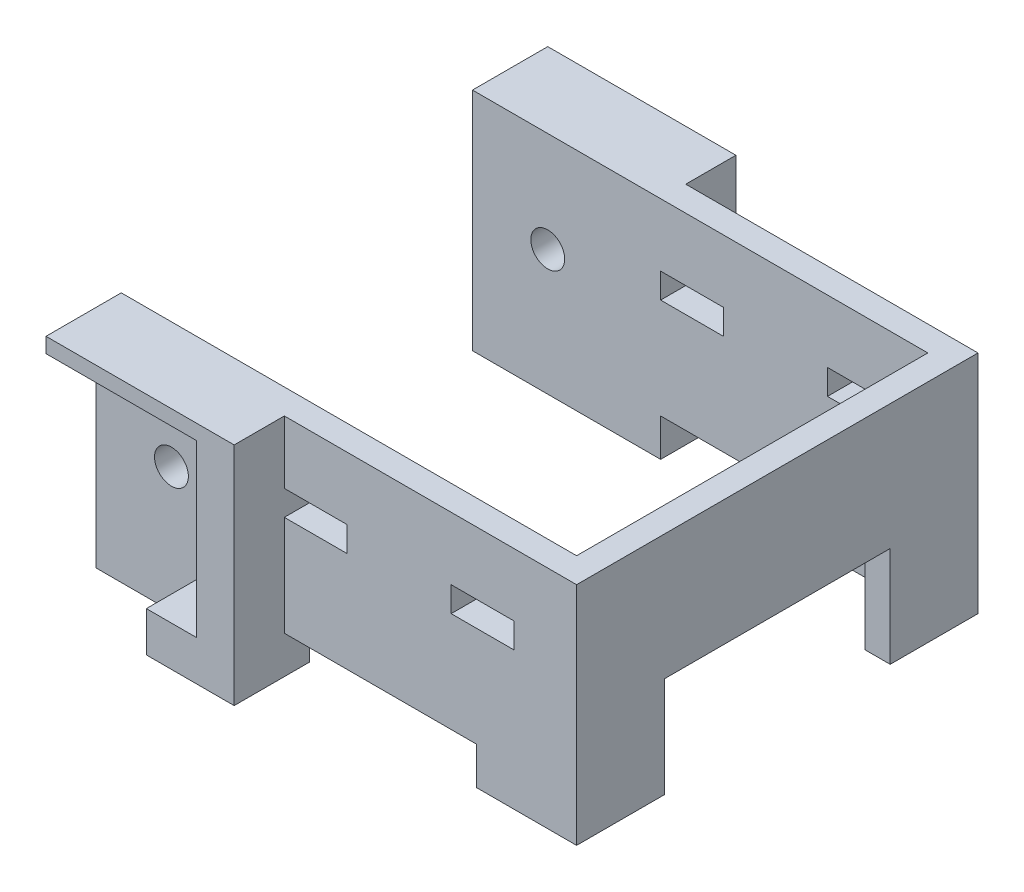
SolidWorks part; units mm, degrees
material "ABS"
ref_plane "Спереди" through (0, 0, 0) normal (0, 0, 1) x (1, 0, 0)
ref_plane "Сверху" through (0, 0, 0) normal (0, 1, 0) x (1, 0, 0)
ref_plane "Справа" through (0, 0, 0) normal (1, 0, 0) x (0, 0, -1)
sketch "Эскиз1" plane through (0, 0, 0) normal (0, 1, 0) x (1, 0, 0)
  line L1 (-19.15, 16) -> (19.15, 16)
  line L2 (-19.15, 16) -> (-19.15, -16)
  line L3 (-19.15, -16) -> (19.15, -16)
  line L4 (19.15, 16) -> (19.15, -16)
  line L5 (-19.15, 16) -> (19.15, -16) construction
  line L6 (-19.15, -16) -> (19.15, 16) construction
  point P0 (0, 0)
  dimension "D1" = 32
  dimension "D2" = 38.3
extrude "Бобышка-Вытянуть1" add sketch "Эскиз1" along normal blind 2
sketch "Эскиз2" plane through (0, 2, 0) normal (0, 1, 0) x (1, 0, 0)
  line L0 (-19.15, 16) -> (19.15, 16)
  line L1 (19.15, 16) -> (19.15, -16)
  line L3 (19.15, -16) -> (-19.15, -16)
  line L4 (-19.15, -16) -> (-19.15, -14)
  line L5 (-19.15, 16) -> (-19.15, -16) construction
  line L6 (-19.15, -14) -> (17.15, -14)
  line L7 (17.15, -14) -> (17.15, 14)
  line L8 (17.15, 14) -> (-19.15, 14)
  line L9 (-19.15, 14) -> (-19.15, 16)
  line L10 (17.15, 14) -> (19.15, 14) construction
  dimension "D1" = 2
extrude "Бобышка-Вытянуть2" add sketch "Эскиз2" along normal blind 75
sketch "Эскиз9" plane through (0, 0, 16) normal (0, 0, 1) x (1, 0, 0)
  line L0 (-19.15, 77) -> (-19.15, 0) construction
  line L1 (-19.15, 0) -> (19.15, 0) construction
  circle A0 centre (-13.15, 69) radius 1.35
  circle A1 centre (-13.15, 10) radius 1.35
  dimension "D1" = 2.7
  dimension "D2" = 59
  dimension "D3" = 6
  dimension "D4" = 10
extrude "Вырез-Вытянуть5" cut sketch "Эскиз9" against normal through all
sketch "Эскиз10" plane through (0, 0, 16) normal (0, 0, 1) x (1, 0, 0)
  line L0 (19.15, 77) -> (19.15, 0) construction
  line L1 (-4.15, 62) -> (11.15, 62)
  line L2 (-4.15, 62) -> (-4.15, 10)
  line L3 (-4.15, 10) -> (11.15, 10)
  line L4 (11.15, 62) -> (11.15, 10)
  line L5 (-19.15, 0) -> (19.15, 0) construction
  line L6 (-19.15, 77) -> (19.15, 77) construction
  line L7 (-19.15, 77) -> (-19.15, 0) construction
  dimension "D1" = 8
  dimension "D2" = 10
  dimension "D3" = 15
  dimension "D4" = 15
extrude "Вырез-Вытянуть6" cut sketch "Эскиз10" against normal through all
sketch "Эскиз11" plane through (0, 0, 0) normal (0, -1, 0) x (1, 0, 0)
  line L0 (-14.15, 11) -> (14.15, 11)
  line L1 (-19.15, 16) -> (19.15, 16) construction
  line L2 (-19.15, 16) -> (-19.15, -16) construction
  line L3 (-19.15, -16) -> (19.15, -16) construction
  line L4 (19.15, 16) -> (19.15, -16) construction
  line L5 (14.15, 11) -> (14.15, -11)
  line L6 (-14.15, -11) -> (14.15, -11)
  line L7 (-14.15, 11) -> (-14.15, -11)
  dimension "D1" = 5
extrude "Вырез-Вытянуть7" cut sketch "Эскиз11" against normal through all
sketch "Эскиз13" plane through (19.15, 0, 0) normal (1, 0, 0) x (0, 0, -1)
  line L1 (-9, 67) -> (9, 67)
  line L2 (-9, 67) -> (-9, 10)
  line L3 (-9, 10) -> (9, 10)
  line L4 (9, 67) -> (9, 10)
  line L5 (-16, 77) -> (16, 77) construction
  line L6 (-9, 67) -> (-16, 67) construction
  line L7 (-16, 77) -> (-16, 0) construction
  line L8 (-16, 0) -> (16, 0) construction
  line L9 (-16, 77) -> (-16, 0) construction
  line L10 (9, 67) -> (16, 67) construction
  line L11 (16, 77) -> (16, 0) construction
  dimension "D1" = 7
  dimension "D2" = 10
  dimension "D3" = 10
extrude "Вырез-Вытянуть8" cut sketch "Эскиз13" against normal through all
sketch "Эскиз14" plane through (0, 0, -16) normal (0, 0, -1) x (-1, 0, 0)
  line L0 (-19.15, 77) -> (19.15, 77) construction
  line L1 (-14.15, 72) -> (-9.15, 72)
  line L2 (-14.15, 72) -> (-14.15, 70)
  line L3 (-14.15, 70) -> (-9.15, 70)
  line L4 (-9.15, 72) -> (-9.15, 70)
  line L5 (-0.85, 72) -> (4.15, 72)
  line L6 (-0.85, 72) -> (-0.85, 70)
  line L7 (-0.85, 70) -> (4.15, 70)
  line L8 (4.15, 72) -> (4.15, 70)
  line L9 (-19.15, 77) -> (-19.15, 0) construction
  line L10 (19.15, 77) -> (19.15, 0) construction
  dimension "D1" = 5
  dimension "D2" = 2
  dimension "D3" = 5
  dimension "D4" = 5
  dimension "D5" = 15
extrude "Вырез-Вытянуть9" cut sketch "Эскиз14" against normal through all
sketch "Эскиз16" plane through (0, 0, 16) normal (0, 0, 1) x (1, 0, 0)
  line L0 (-19.15, 77) -> (-19.15, 0) construction
  line L1 (-19.15, 0) -> (-4.15, 0)
  line L2 (-19.15, 0) -> (-19.15, 3.2)
  line L3 (-19.15, 3.2) -> (-7.15, 3.2)
  line L4 (-7.15, 16.8) -> (-7.15, 3.2)
  line L5 (-19.15, 16.8) -> (-7.15, 16.8)
  line L6 (-19.15, 16.8) -> (-19.15, 19.8)
  line L7 (-19.15, 19.8) -> (-4.15, 19.8)
  line L8 (-4.15, 19.8) -> (-4.15, 0)
  line L9 (-4.15, 62) -> (-4.15, 10) construction
  dimension "D1" = 3.2
  dimension "D2" = 3
  dimension "D3" = 13.6
  dimension "D4" = 3
extrude "Бобышка-Вытянуть3" add sketch "Эскиз16" along normal blind 4
mirror "Зеркальное отражение1" about plane through (0, 0, 0) normal (0, 0, 1) of "Бобышка-Вытянуть3"
sketch "Эскиз18" plane through (0, 0, 16) normal (0, 0, 1) x (1, 0, 0)
  line L0 (-19.15, 62.2) -> (-19.15, 59)
  line L1 (-19.15, 77) -> (-19.15, 19.8) construction
  line L2 (-19.15, 59) -> (-4.15, 59)
  line L3 (-4.15, 59) -> (-4.15, 77)
  line L4 (-4.15, 77) -> (-19.15, 77)
  line L5 (-19.15, 77) -> (-19.15, 75.8)
  line L6 (-19.15, 75.8) -> (-7.15, 75.8)
  line L7 (-7.15, 75.8) -> (-7.15, 62.2)
  line L8 (-7.15, 62.2) -> (-19.15, 62.2)
  line L9 (-19.15, 77) -> (19.15, 77) construction
  line L10 (-4.15, 62) -> (-4.15, 19.8) construction
  circle A1 centre (-13.15, 69) radius 1.35 construction
  point P14 (0, 0)
  dimension "D1" = 6.8
  dimension "D2" = 6.8
  dimension "D3" = 6
  dimension "D4" = 3.2
extrude "Бобышка-Вытянуть4" add sketch "Эскиз18" along normal blind 4
mirror "Зеркальное отражение2" about plane through (0, 0, 0) normal (0, 0, 1) of "Бобышка-Вытянуть4"
sketch "Эскиз19" plane through (0, 0, 20) normal (0, 0, 1) x (1, 0, 0)
  line L0 (-19.15, 16.8) -> (-7.15, 16.8) construction
  line L1 (-19.15, 62.2) -> (-11.15, 62.2)
  line L2 (-19.15, 62.2) -> (-19.15, 16.8)
  line L3 (-19.15, 16.8) -> (-11.15, 16.8)
  line L4 (-11.15, 62.2) -> (-11.15, 16.8)
  dimension "D1" = 8
extrude "Вырез-Вытянуть10" cut sketch "Эскиз19" against normal up to surface (4 mm away) up to face at (11.65, 71, 16)
sketch "Эскиз20" plane through (0, 0, 0) normal (0, -1, 0) x (1, 0, 0)
  line L1 (-19.15, 20) -> (21.5637, 20)
  line L2 (-19.15, 20) -> (-19.15, -21.3765)
  line L3 (-19.15, -21.3765) -> (21.5637, -21.3765)
  line L4 (21.5637, 20) -> (21.5637, -21.3765)
extrude "Вырез-Вытянуть11" cut sketch "Эскиз20" against normal up to surface (59 mm away) up to face at (-7.65, 59, 18)
